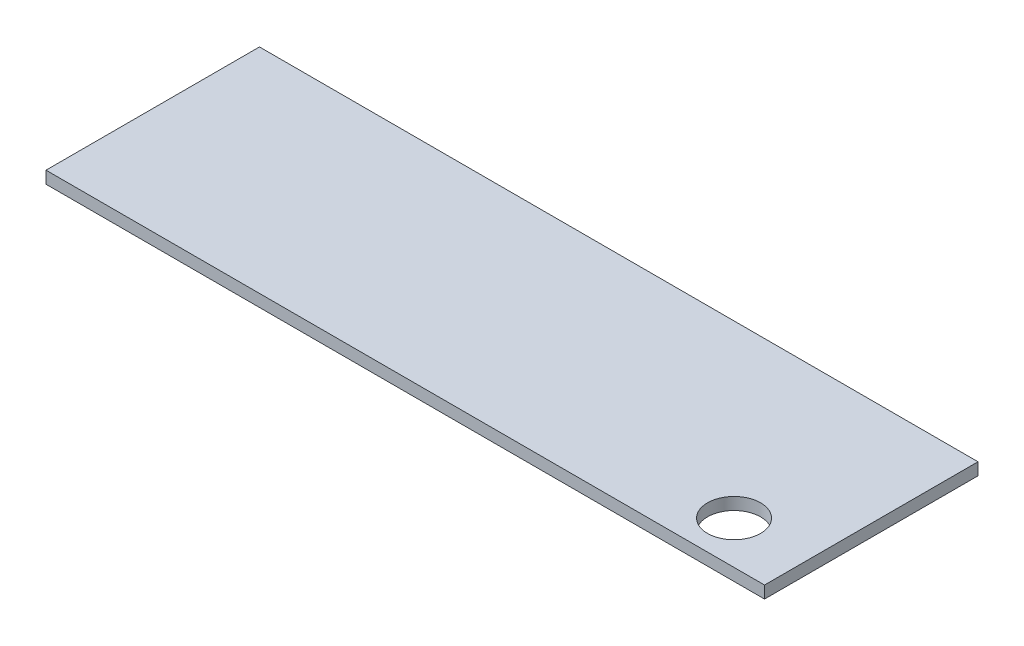
SolidWorks part; units mm, degrees
ref_plane "Front Plane" through (0, 0, 0) normal (0, 0, 1) x (1, 0, 0)
ref_plane "Top Plane" through (0, 0, 0) normal (0, 1, 0) x (1, 0, 0)
ref_plane "Right Plane" through (0, 0, 0) normal (1, 0, 0) x (0, 0, -1)
sketch "Sketch1" plane through (0, 0, 0) normal (0, 1, 0) x (1, 0, 0)
  line L0 (-100.0226, 35) -> (17.7871, 35)
  line L1 (17.7871, 35) -> (17.7871, 0)
  line L2 (17.7871, 0) -> (-100.0226, 0)
  line L3 (-100.0226, 0) -> (-100.0226, 35)
  circle A0 centre (5.7871, 7) radius 4.35
  point P9 (10.5061, 9.4445)
  dimension "D5" = 8.7
  dimension "D1" = 117.8097
  dimension "D2" = 35
  dimension "D3" = 7
  dimension "D4" = 12
extrude "Boss-Extrude1" add sketch "Sketch1" along normal blind 2
